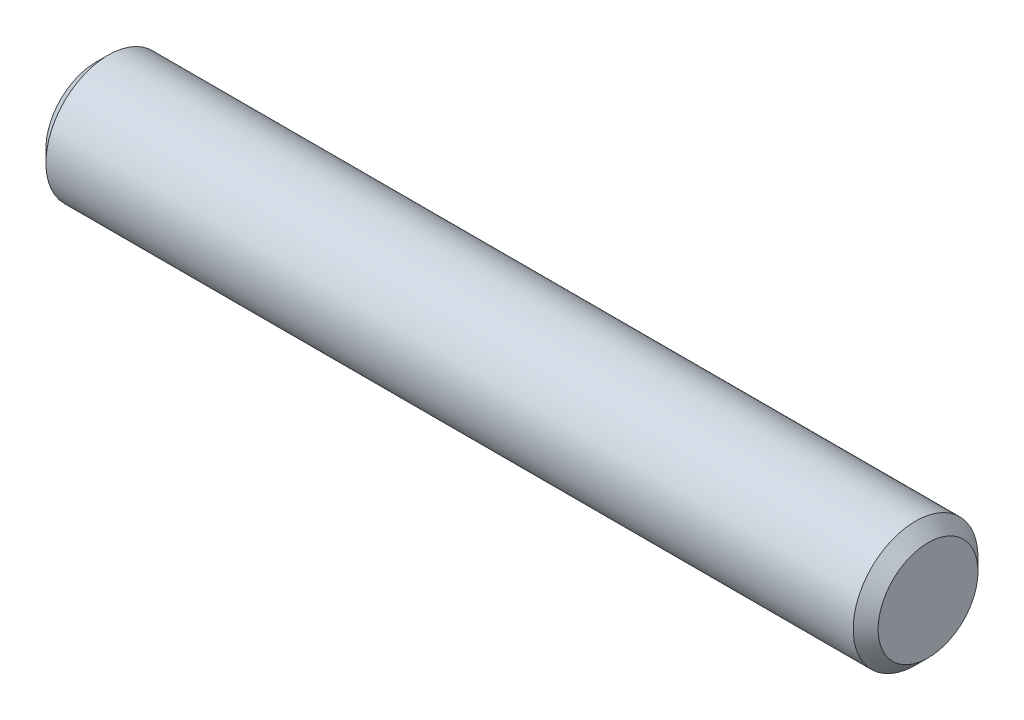
SolidWorks part; units mm, degrees
material "Plain Carbon Steel"
ref_plane "Front" through (0, 0, 0) normal (0, 0, 1) x (1, 0, 0)
ref_plane "Top" through (0, 0, 0) normal (0, 1, 0) x (1, 0, 0)
ref_plane "Right" through (0, 0, 0) normal (1, 0, 0) x (0, 0, -1)
sketch "Sketch1" plane through (0, 0, 0) normal (1, 0, 0) x (0, 0, -1)
  circle A0 centre (0, 0) radius 1.5 construction
  dimension "Diameter" = 3
sketch "Sketch2" plane through (0, 0, 0) normal (0, 0, 1) x (1, 0, 0)
  line L1 (-10, 1.5) -> (10, 1.5) construction
  line L2 (-10, 1.5) -> (-10, -1.5) construction
  line L3 (-10, -1.5) -> (10, -1.5) construction
  line L4 (10, 1.5) -> (10, -1.5) construction
  line L5 (0, -1.5) -> (0, 1.5) construction
  line L6 (-10, 0) -> (10, 0) construction
  point P0 (0, 0)
  dimension "Length" = 20
sketch "Sketch3" plane through (0, 0, 0) normal (1, 0, 0) x (0, 0, -1)
  circle A0 centre (0, 0) radius 1.5 construction
  circle A1 centre (0, 0) radius 1.5
extrude "Extrude1" add sketch "Sketch3" against normal up to vertex (10 mm away) and the other way up to vertex (10 mm away) up to point (-10, 0, 0) other way up to point (10, 0, 0)
chamfer "Chamfer1" distance 0.3 angle 45 2 edges at (10, 0, -1.5) (-10, 0, -1.5)
equation "\"D1@Chamfer1\"=\"Diameter@Sketch1\"*.1"
equation "\"D1@Fillet1\"=\"Diameter@Sketch1\"*.1"
